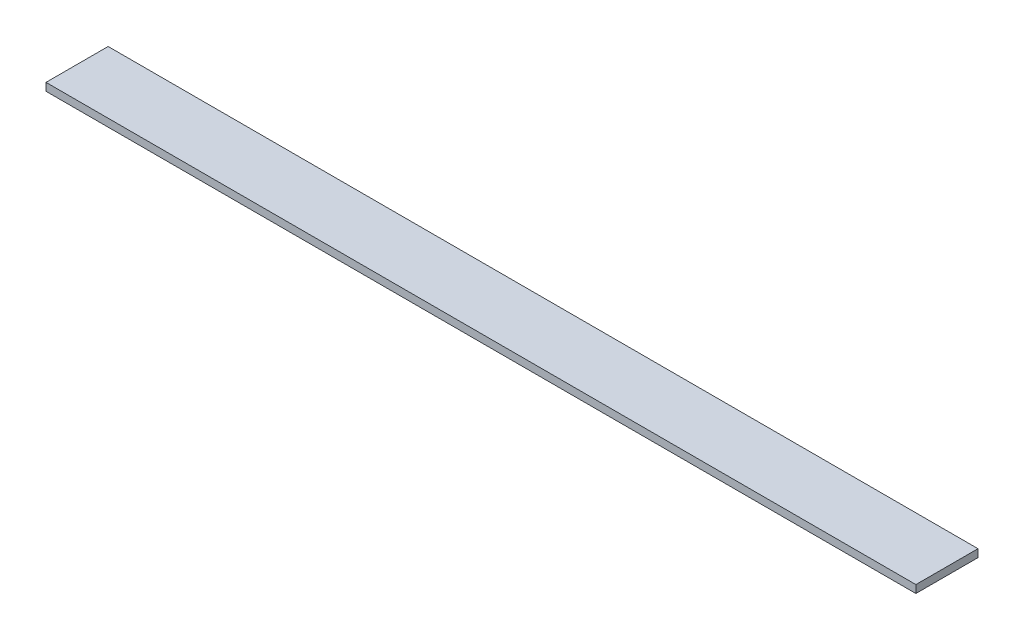
SolidWorks part; units mm, degrees
material "6061-T6 (SS)"
ref_plane "Front Plane" through (0, 0, 0) normal (0, 0, 1) x (1, 0, 0)
ref_plane "Top Plane" through (0, 0, 0) normal (0, 1, 0) x (1, 0, 0)
ref_plane "Right Plane" through (0, 0, 0) normal (1, 0, 0) x (0, 0, -1)
sketch "Sketch2" plane through (0, 0, 0) normal (0, 1, 0) x (1, 0, 0)
  line L1 (-177.8, -12.7) -> (177.8, -12.7)
  line L2 (-177.8, -12.7) -> (-177.8, 12.7)
  line L3 (-177.8, 12.7) -> (177.8, 12.7)
  line L4 (177.8, -12.7) -> (177.8, 12.7)
  line L5 (-177.8, -12.7) -> (177.8, 12.7) construction
  line L6 (-177.8, 12.7) -> (177.8, -12.7) construction
  point P0 (0, 0)
  dimension "D1" = 355.6
  dimension "D2" = 25.4
extrude "Boss-Extrude1" add sketch "Sketch2" along normal blind 3.175
